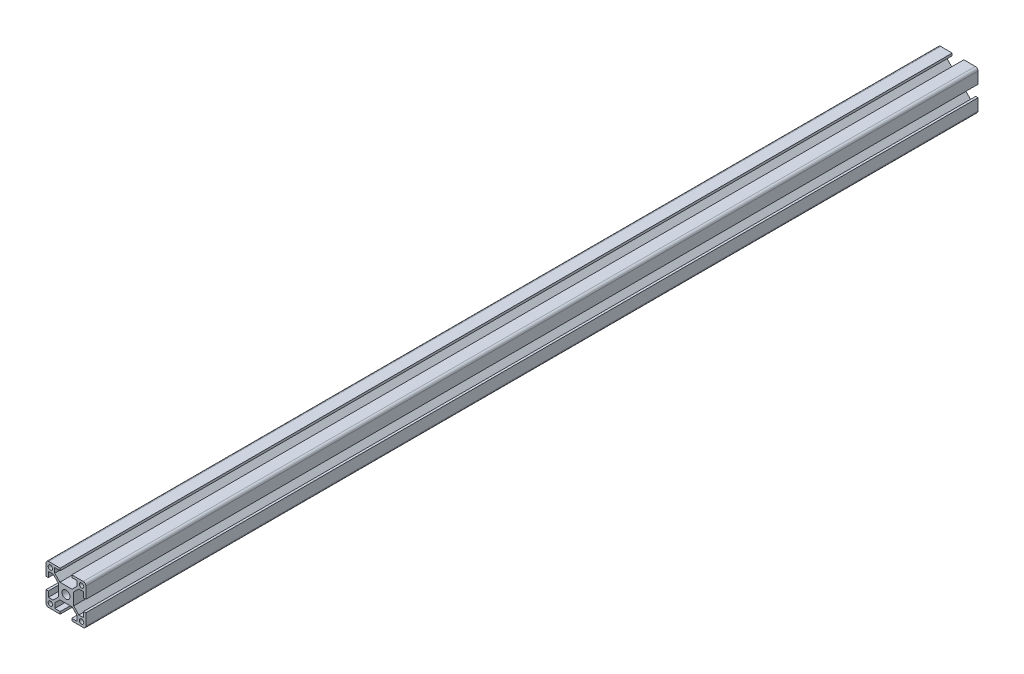
SolidWorks part; units mm, degrees
ref_plane "Front Plane" through (0, 0, 0) normal (0, 0, 1) x (1, 0, 0)
ref_plane "Top Plane" through (0, 0, 0) normal (0, 1, 0) x (1, 0, 0)
ref_plane "Right Plane" through (0, 0, 0) normal (1, 0, 0) x (0, 0, -1)
sketch "Sketch1" plane through (0, 0, 0) normal (0, 0, 1) x (1, 0, 0)
  line L0 (-8.46, 9.66) -> (-4.55, 5.75)
  line L1 (-15, -15) -> (-4.35, -15)
  line L2 (-15, -15) -> (-15, -4.35)
  line L3 (-15, 15) -> (-4.35, 15)
  line L4 (15, -15) -> (15, -4.35)
  line L5 (-15, -15) -> (15, 15) construction
  line L6 (-15, 15) -> (15, -15) construction
  line L7 (-4.5783, -5.75) -> (4.6181, -5.75)
  line L8 (-5.75, -4.55) -> (-5.75, 4.55)
  line L9 (-4.55, 5.75) -> (4.55, 5.75)
  line L10 (5.75, -4.55) -> (5.75, 4.55)
  line L11 (-5.75, -5.75) -> (5.75, 5.75) construction
  line L12 (-5.75, 5.75) -> (5.75, -5.75) construction
  line L13 (-8.46, 9.66) -> (-8.46, 13.26)
  line L14 (-8.46, 13.26) -> (-4.35, 13.26)
  line L15 (-4.35, 13.26) -> (-4.35, 15)
  line L16 (-9.66, 8.46) -> (-5.75, 4.55)
  line L17 (-9.66, 8.46) -> (-13.26, 8.46)
  line L18 (-13.26, 8.46) -> (-13.26, 4.35)
  line L19 (-13.26, 4.35) -> (-15, 4.35)
  line L20 (9.66, 8.46) -> (5.75, 4.55)
  line L21 (8.46, 9.66) -> (8.46, 13.26)
  line L22 (8.46, 13.26) -> (4.35, 13.26)
  line L23 (4.35, 13.26) -> (4.35, 15)
  line L24 (8.46, 9.66) -> (4.55, 5.75)
  line L25 (9.66, 8.46) -> (13.26, 8.46)
  line L26 (13.26, 8.46) -> (13.26, 4.35)
  line L27 (13.26, 4.35) -> (15, 4.35)
  line L28 (9.66, -8.46) -> (5.75, -4.55)
  line L29 (-9.66, -8.46) -> (-13.26, -8.46)
  line L30 (-13.26, -8.46) -> (-13.26, -4.35)
  line L31 (-13.26, -4.35) -> (-15, -4.35)
  line L32 (-9.66, -8.46) -> (-5.75, -4.55)
  line L33 (-8.4202, -9.5919) -> (-8.4202, -13.26)
  line L34 (-8.4202, -13.26) -> (-4.35, -13.26)
  line L35 (-4.35, -13.26) -> (-4.35, -15)
  line L36 (-8.4202, -9.5919) -> (-4.5783, -5.75)
  line L37 (9.66, -8.46) -> (13.26, -8.46)
  line L38 (13.26, -8.46) -> (13.26, -4.35)
  line L39 (13.26, -4.35) -> (15, -4.35)
  line L40 (8.46, -9.5919) -> (4.6181, -5.75)
  line L41 (8.46, -9.5919) -> (8.46, -13.26)
  line L42 (8.46, -13.26) -> (4.35, -13.26)
  line L43 (4.35, -13.26) -> (4.35, -15)
  line L44 (-15, 4.35) -> (-15, 15)
  line L45 (15, 4.35) -> (15, 15)
  line L46 (4.35, -15) -> (15, -15)
  line L47 (4.35, 15) -> (15, 15)
  circle A0 centre (0, 0) radius 3
  circle A1 centre (11.73, 11.73) radius 1.65
  circle A2 centre (11.73, -11.73) radius 1.65
  circle A3 centre (-11.73, -11.73) radius 1.65
  circle A4 centre (-11.73, 11.73) radius 1.65
  point P0 (0, 0)
  dimension "D3" = 6
  dimension "D10" = 3.3
  dimension "D1" = 30
  dimension "D2" = 30
  dimension "D4" = 11.5
  dimension "D5" = 11.5
  dimension "D6" = 10.65
  dimension "D7" = 4.11
  dimension "D8" = 1.74
  dimension "D9" = 3.6
  dimension "D11" = 3.27
  dimension "D12" = 3.27
  dimension "D13" = 3.27
  dimension "D14" = 3.27
  dimension "D15" = 3.27
  dimension "D16" = 3.27
  dimension "D17" = 3.27
  dimension "D18" = 3.27
extrude "Boss-Extrude1" add sketch "Sketch1" along normal blind 670
fillet "Fillet1" radius 2 4 edges at (-15, -15, 335) (15, -15, 335) (15, 15, 335) (-15, 15, 335)
